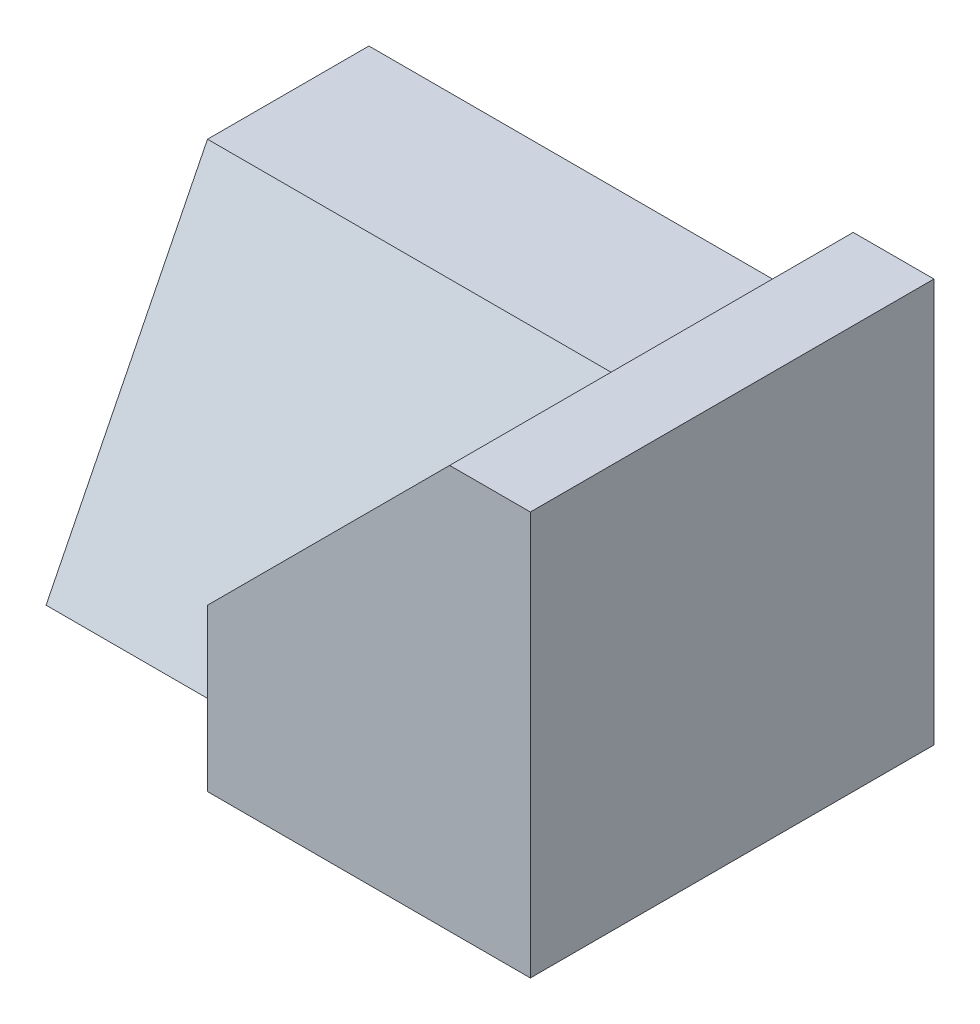
SolidWorks part; units mm, degrees
ref_plane "Front Plane" through (0, 0, 0) normal (0, 0, 1) x (1, 0, 0)
ref_plane "Top Plane" through (0, 0, 0) normal (0, 1, 0) x (1, 0, 0)
ref_plane "Right Plane" through (0, 0, 0) normal (1, 0, 0) x (0, 0, -1)
sketch "Sketch1" plane through (0, 0, 0) normal (0, 0, 1) x (1, 0, 0)
  line L1 (0, 0) -> (70, 0)
  line L2 (0, 0) -> (0, 50)
  line L3 (0, 50) -> (70, 50)
  line L4 (70, 0) -> (70, 50)
  dimension "D1" = 70
  dimension "D2" = 50
extrude "Boss-Extrude1" add sketch "Sketch1" along normal blind 50
sketch "Sketch2" plane through (0, 0, 50) normal (0, 0, 1) x (1, 0, 0)
  line L0 (0, 40) -> (50, 40)
  line L1 (0, 50) -> (0, 0) construction
  line L2 (50, 40) -> (60, 50)
  line L3 (70, 50) -> (0, 50) construction
  line L4 (60, 50) -> (0, 50)
  line L5 (0, 50) -> (0, 40)
  dimension "D1" = 10
  dimension "D2" = 10
  dimension "D3" = 10
extrude "Cut-Extrude1" cut sketch "Sketch2" against normal blind 50
sketch "Sketch3" plane through (0, 0, 50) normal (0, 0, 1) x (1, 0, 0)
  line L0 (50, 40) -> (30, 20)
  line L1 (30, 20) -> (30, 0)
  line L2 (0, 0) -> (70, 0) construction
  line L3 (30, 0) -> (0, 0)
  line L4 (0, 0) -> (0, 40)
  line L5 (0, 40) -> (50, 40)
  dimension "D1" = 30
  dimension "D2" = 20
extrude "Cut-Extrude2" cut sketch "Sketch3" against normal blind 30
sketch3d "3DSketch2"
  line L0 (30, 0, 40) -> (0, 0, 40)
  line L1 (30, 0, 20) -> (30, 0, 50) construction
  dimension "D1" = 20
  dimension "D2" = 20
ref_plane "Plane1" through (0, 16, 32) normal (0, -0.4472, -0.8944) x (-1, 0, 0)
sketch "Sketch7" plane through (0, 16, 32) normal (0, -0.4472, -0.8944) x (-1, 0, 0)
  line L0 (0, 26.8328) -> (-50, 26.8328)
  line L1 (-50, 26.8328) -> (-30, -17.8885)
  line L2 (-30, -17.8885) -> (0, -17.8885)
  line L3 (0, -17.8885) -> (0, 26.8328)
extrude "Boss-Extrude2" add sketch "Sketch7" along normal blind 30
sketch "Sketch8" plane through (0, 0, 0) normal (0, 0, -1) x (-1, 0, 0)
  line L1 (-70, 0) -> (0, 0)
  line L2 (-70, 0) -> (-70, 40)
  line L3 (-70, 40) -> (0, 40)
  line L4 (0, 0) -> (0, 40)
extrude "Cut-Extrude7" cut sketch "Sketch8" along normal blind 30
sketch "Sketch9" plane through (0, 0, 0) normal (0, -1, 0) x (1, 0, 0)
  line L1 (70, 0) -> (0, 0)
  line L2 (70, 0) -> (70, 50)
  line L3 (70, 50) -> (0, 50)
  line L4 (0, 0) -> (0, 50)
  dimension "D1" = 50
  dimension "D2" = 70
extrude "Cut-Extrude8" cut sketch "Sketch9" along normal blind 30
